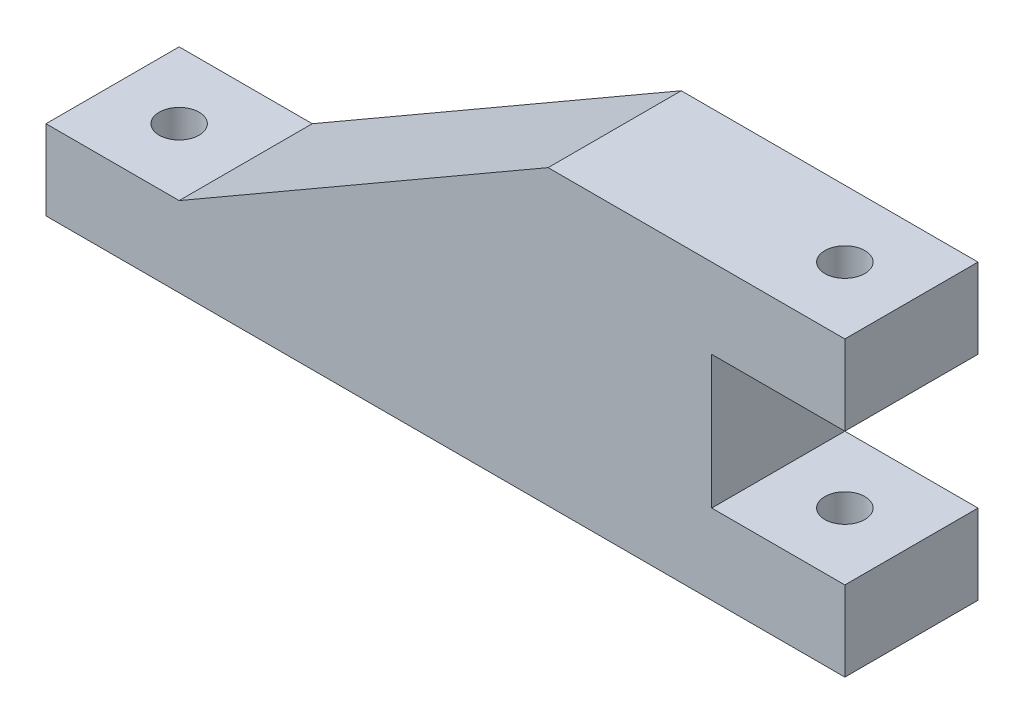
SolidWorks part; units mm, degrees
material "Chrome Stainless Steel"
ref_plane "Front Plane" through (0, 0, 0) normal (0, 0, 1) x (1, 0, 0)
ref_plane "Top Plane" through (0, 0, 0) normal (0, 1, 0) x (1, 0, 0)
ref_plane "Right Plane" through (0, 0, 0) normal (1, 0, 0) x (0, 0, -1)
sketch "Sketch1" plane through (0, 0, 0) normal (0, 0, 1) x (1, 0, 0)
  line L0 (-300, 0) -> (0, 0)
  line L1 (0, 0) -> (0, 30)
  line L2 (0, 30) -> (-50, 30)
  line L3 (-50, 30) -> (-50, 80)
  line L4 (-50, 80) -> (0, 80)
  line L5 (0, 80) -> (0, 110)
  line L6 (0, 110) -> (-111.4359, 110)
  line L7 (-111.4359, 110) -> (-250, 30)
  line L8 (-250, 30) -> (-300, 30)
  line L9 (-300, 30) -> (-300, 0)
  dimension "D1" = 300
  dimension "D2" = 30
  dimension "D3" = 50
  dimension "D4" = 50
  dimension "D5" = 30
  dimension "D6" = 30
  dimension "D7" = 30
  dimension "D8" = 50
extrude "Boss-Extrude1" add sketch "Sketch1" along normal blind 50
sketch "Sketch2" plane through (0, 30, 0) normal (0, 1, 0) x (1, 0, 0)
  line L0 (-300, -50) -> (-300, 0) construction
  circle A0 centre (-275, -25) radius 7.5
  circle A1 centre (-25, -25) radius 7.5
  dimension "D1" = 15
  dimension "D2" = 15
  dimension "D3" = 25
  dimension "D4" = 25
extrude "Cut-Extrude1" cut sketch "Sketch2" against normal through all both and the other way through all
